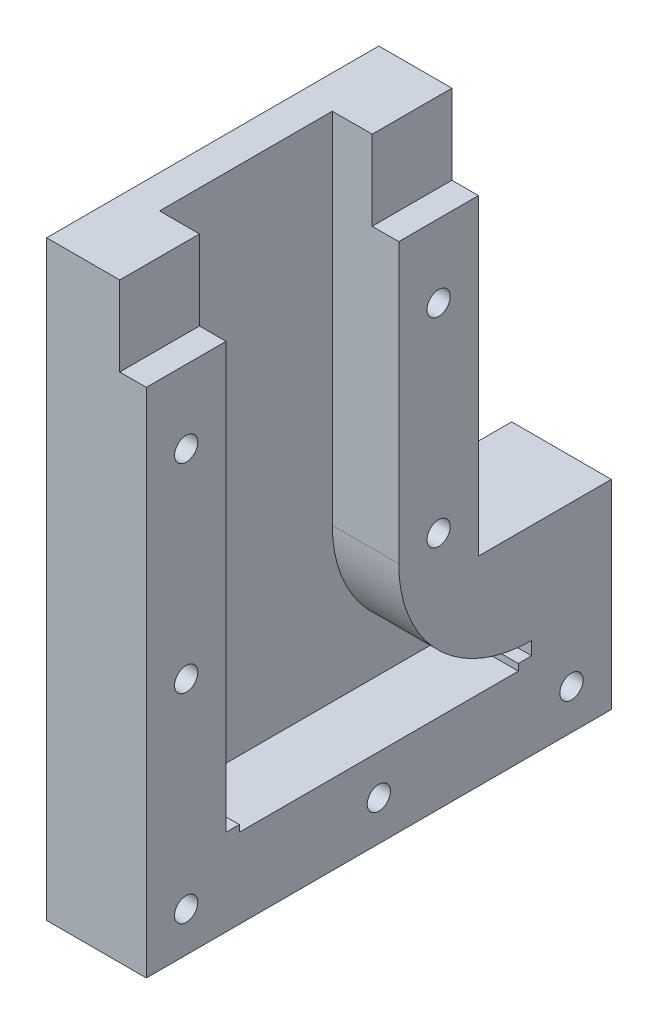
SolidWorks part; units mm, degrees
ref_plane "正面" through (0, 0, 0) normal (0, 0, 1) x (1, 0, 0)
ref_plane "平面" through (0, 0, 0) normal (0, 1, 0) x (1, 0, 0)
ref_plane "右側面" through (0, 0, 0) normal (1, 0, 0) x (0, 0, -1)
sketch "ｽｹｯﾁ1" plane through (0, 0, 0) normal (1, 0, 0) x (0, 0, -1)
  line L0 (25, 44.5) -> (25, -14.5)
  line L1 (-25, 44.5) -> (25, 44.5)
  line L2 (-25, 44.5) -> (-25, -44.5)
  line L3 (-25, -44.5) -> (25, -44.5)
  line L5 (-25, 44.5) -> (25, -44.5) construction
  line L6 (-25, -44.5) -> (25, 44.5) construction
  line L7 (25, -14.5) -> (45, -14.5)
  line L9 (25, -44.5) -> (45, -44.5)
  line L10 (45, -14.5) -> (45, -44.5)
  point P0 (0, 0)
  dimension "D1" = 89
  dimension "D2" = 50
  dimension "D3" = 20
  dimension "D4" = 30
extrude "ﾎﾞｽ - 押し出し2" add sketch "ｽｹｯﾁ1" along normal blind 15
sketch "ｽｹｯﾁ4" plane through (15, 0, 0) normal (1, 0, 0) x (0, 0, -1)
  line L0 (25, 44.5) -> (-25, 44.5) construction
  line L1 (-13, 44.5) -> (13, 44.5)
  line L2 (-13, 44.5) -> (-13, -32.5)
  line L3 (-13, -32.5) -> (13, -32.5)
  line L4 (13, 44.5) -> (13, -32.5)
  line L5 (-25, 44.5) -> (-25, -44.5) construction
  line L6 (25, -14.5) -> (25, 44.5) construction
  dimension "D1" = 77
  dimension "D2" = 12
  dimension "D3" = 12
extrude "ｶｯﾄ - 押し出し3" cut sketch "ｽｹｯﾁ4" against normal blind 10
sketch "ｽｹｯﾁ5" plane through (15, 0, 0) normal (1, 0, 0) x (0, 0, -1)
  line L0 (13, -32.5) -> (13, 44.5) construction
  line L1 (-13, -32.5) -> (13, -32.5) construction
  line L2 (13, -32.5) -> (13, -9.5)
  line L4 (33, -29.5) -> (33, -32.5)
  line L5 (33, -32.5) -> (13, -32.5)
  arc A0 (13, -9.5) -> (33, -29.5) centre (33, -9.5) ccw
  point P0 (33, -9.5)
  dimension "D1" = 20
  dimension "D2" = 23
extrude "ｶｯﾄ - 押し出し5" cut sketch "ｽｹｯﾁ5" against normal blind 10
sketch "ｽｹｯﾁ6" plane through (15, 0, 0) normal (1, 0, 0) x (0, 0, -1)
  line L0 (-13, 44.5) -> (-13, -32.5) construction
  line L1 (-25, 44.5) -> (-13, 44.5)
  line L2 (-25, 44.5) -> (-25, 32.5)
  line L3 (-25, 32.5) -> (-13, 32.5)
  line L4 (-13, 44.5) -> (-13, 32.5)
  line L5 (25, -14.5) -> (25, 44.5) construction
  line L6 (13, 44.5) -> (25, 44.5)
  line L7 (13, 44.5) -> (13, 32.5)
  line L8 (13, 32.5) -> (25, 32.5)
  line L9 (25, 44.5) -> (25, 32.5)
  dimension "D1" = 12
  dimension "D2" = 12
extrude "ｶｯﾄ - 押し出し6" cut sketch "ｽｹｯﾁ6" against normal blind 4
sketch "ｽｹｯﾁ7" plane through (5, 0, 0) normal (1, 0, 0) x (0, 0, -1)
  line L1 (-13, -32.5) -> (-11, -32.5)
  line L2 (-13, -32.5) -> (-13, -30.5)
  line L3 (-13, -30.5) -> (-11, -30.5)
  line L4 (-11, -32.5) -> (-11, -30.5)
  line L5 (33, -32.5) -> (31, -32.5)
  line L6 (33, -32.5) -> (33, -30.5)
  line L7 (33, -30.5) -> (31, -30.5)
  line L8 (31, -32.5) -> (31, -30.5)
  dimension "D1" = 2
  dimension "D2" = 2
  dimension "D3" = 2
  dimension "D4" = 2
extrude "ﾎﾞｽ - 押し出し5" add sketch "ｽｹｯﾁ7" along normal blind 3
sketch "ｽｹｯﾁ8" plane through (8, 0, 0) normal (1, 0, 0) x (0, 0, -1)
  line L0 (-11, -32.5) -> (-11, -30.5) construction
  line L1 (-13, -32.5) -> (-11, -32.5)
  line L2 (-13, -32.5) -> (-13, -31.5)
  line L3 (-13, -31.5) -> (-11, -31.5)
  line L4 (-11, -32.5) -> (-11, -31.5)
  line L5 (31, -30.5) -> (31, -32.5) construction
  line L6 (33, -32.5) -> (31, -32.5)
  line L7 (33, -32.5) -> (33, -31.5)
  line L8 (33, -31.5) -> (31, -31.5)
  line L9 (31, -32.5) -> (31, -31.5)
extrude "ﾎﾞｽ - 押し出し6" add sketch "ｽｹｯﾁ8" along normal blind 7
sketch "ｽｹｯﾁ9" plane through (15, 0, 0) normal (1, 0, 0) x (0, 0, -1)
  line L0 (-13, 44.5) -> (-25, 44.5) construction
  line L1 (-25, 32.5) -> (-25, -44.5) construction
  line L2 (-25, -44.5) -> (45, -44.5) construction
  line L3 (45, -44.5) -> (45, -14.5) construction
  line L4 (25, -14.5) -> (25, 32.5) construction
  line L5 (25, 44.5) -> (13, 44.5) construction
  circle A0 centre (-19, 21.5) radius 1.75
  circle A1 centre (-19, -8.5) radius 1.75
  circle A2 centre (-19, -38.5) radius 1.75
  circle A3 centre (10, -38.5) radius 1.75
  circle A4 centre (39, -38.5) radius 1.75
  circle A5 centre (19, -8.5) radius 1.75
  circle A6 centre (19, 21.5) radius 1.75
  dimension "D1" = 3.5
  dimension "D4" = 30
  dimension "D5" = 3.5
  dimension "D7" = 3.5
  dimension "D10" = 3.5
  dimension "D12" = 3.5
  dimension "D16" = 3.5
  dimension "D18" = 3.5
  dimension "D2" = 23
  dimension "D3" = 6
  dimension "D6" = 6
  dimension "D8" = 6
  dimension "D9" = 6
  dimension "D11" = 6
  dimension "D13" = 6
  dimension "D14" = 6
  dimension "D15" = 29
  dimension "D17" = 6
  dimension "D19" = 6
  dimension "D20" = 23
  dimension "D21" = 30
extrude "ｶｯﾄ - 押し出し7" cut sketch "ｽｹｯﾁ9" against normal through all
